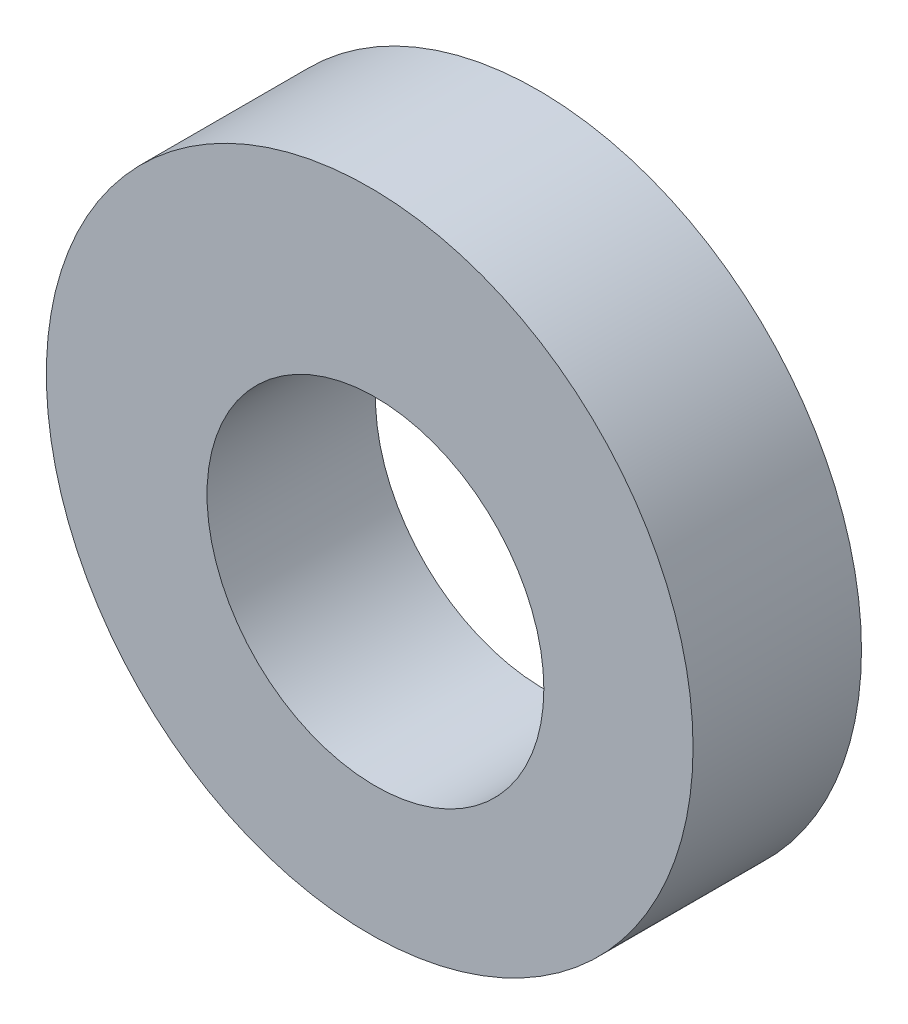
SolidWorks part; units mm, degrees
material "AISI 316 Stainless Steel Sheet (SS)"
ref_plane "Front Plane" through (0, 0, 0) normal (0, 0, 1) x (1, 0, 0)
ref_plane "Top Plane" through (0, 0, 0) normal (0, 1, 0) x (1, 0, 0)
ref_plane "Right Plane" through (0, 0, 0) normal (1, 0, 0) x (0, 0, -1)
sketch "Sketch1" plane through (0, 0, 0) normal (0, 0, 1) x (1, 0, 0)
  circle A0 centre (0, 0) radius 9.6
  dimension "D1" = 19.2
extrude "Boss-Extrude1" add sketch "Sketch1" along normal blind 5
sketch "Sketch2" plane through (0, 0, 5) normal (0, 0, 1) x (1, 0, 0)
  circle A0 centre (0.17, -0.7116) radius 5
  circle A1 centre (0, 0) radius 9.6 construction
  point P2 (0, -9.6)
  point P6 (0, 9.6)
  point P7 (9.6, 0)
  dimension "D1" = 10
  dimension "D2" = 8.89
  dimension "D3" = 9.43
extrude "Cut-Extrude1" cut sketch "Sketch2" against normal blind 5
sketch "Sketch3" plane through (0, 0, 0) normal (0, 0, -1) x (-1, 0, 0)
  line L0 (-0.0009, 9.6) -> (-0.0009, 4.2855) construction
  circle A0 centre (-0.17, -0.7116) radius 5 construction
  circle A1 centre (0, 0) radius 9.6 construction
  point P0 (-0.0009, 4.2855)
  point P1 (-0.0009, 9.6)
  point P4 (0, -9.6)
